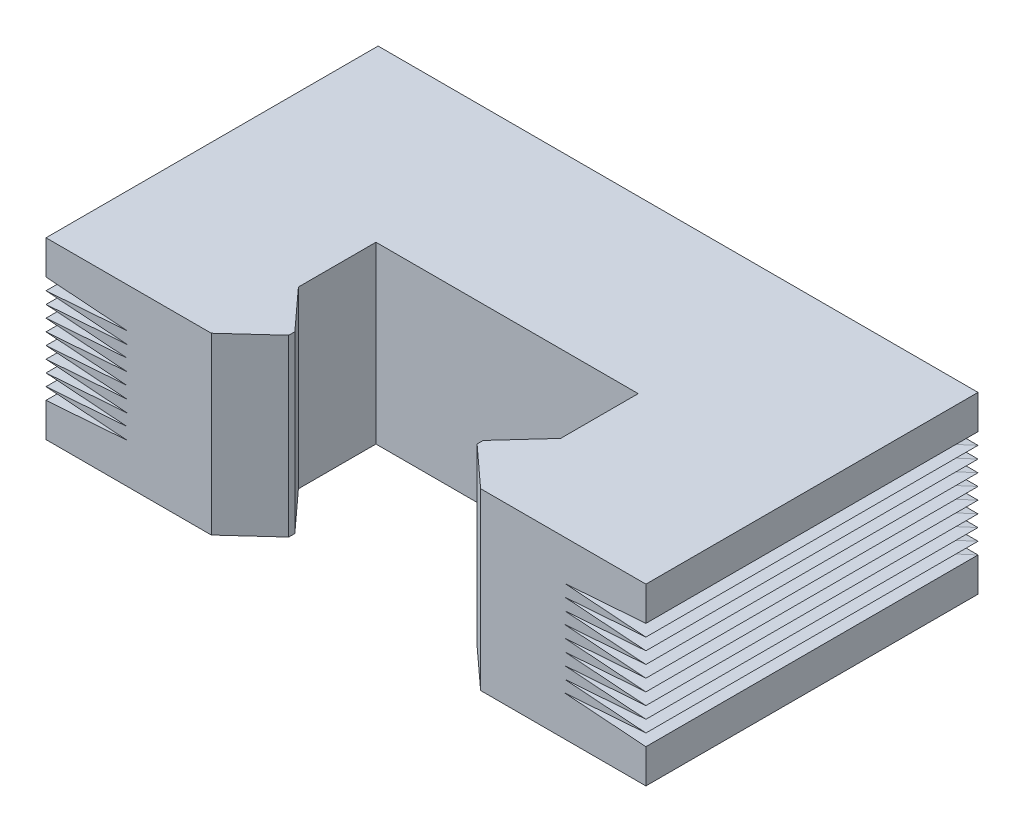
SolidWorks part; units mm, degrees
ref_plane "Front Plane" through (0, 0, 0) normal (0, 0, 1) x (1, 0, 0)
ref_plane "Top Plane" through (0, 0, 0) normal (0, 1, 0) x (1, 0, 0)
ref_plane "Right Plane" through (0, 0, 0) normal (1, 0, 0) x (0, 0, -1)
sketch "Sketch3" plane through (0, 0, 0) normal (0, 1, 0) x (1, 0, 0)
  line L0 (0, 0) -> (0, 15.96) construction
  line L1 (-28, 15.96) -> (28, 15.96)
  line L2 (28, 15.96) -> (28, -15.04)
  line L3 (28, -15.04) -> (12.57, -15.04)
  line L4 (12.57, -15.04) -> (8.79, -11.59)
  line L5 (8.79, -11.59) -> (8.79, -11.02)
  line L6 (8.79, -11.02) -> (12.24, -7.24)
  line L7 (12.24, -7.24) -> (12.24, 0)
  line L8 (12.24, 0) -> (-12.24, 0)
  line L9 (-12.24, -7.24) -> (-12.24, 0)
  line L10 (-8.79, -11.02) -> (-12.24, -7.24)
  line L11 (-8.79, -11.59) -> (-8.79, -11.02)
  line L12 (-12.57, -15.04) -> (-8.79, -11.59)
  line L13 (-28, -15.04) -> (-12.57, -15.04)
  line L14 (-28, 15.96) -> (-28, -15.04)
  point P12 (0, 0)
  point P18 (12.24, 7.1402)
  point P19 (0, 0)
  dimension "D1" = 56
  dimension "D2" = 31
  dimension "D3" = 24.48
  dimension "D4" = 15.04
  dimension "D5" = 0.57
  dimension "D6" = 15.43
  dimension "D7" = 7.8
  dimension "D8" = 15.76
  dimension "D9" = 3.78
sketch "Sketch4" plane through (0, 0, 0) normal (0, 0, 1) x (1, 0, 0)
  line L0 (28, 0) -> (28, -3.175)
  line L1 (28, 0) -> (12.57, 0) construction
  line L2 (28, -3.175) -> (20.4001, -3.7287)
  line L3 (20.4001, -3.7287) -> (28, -4.2824)
  line L4 (28, -4.2824) -> (20.4001, -4.8361)
  line L5 (20.4001, -4.8361) -> (28, -5.3898)
  line L6 (28, -5.3898) -> (20.4001, -5.9435)
  line L7 (20.4001, -5.9435) -> (28, -6.4972)
  line L8 (28, -6.4972) -> (20.4001, -7.051)
  line L9 (20.4001, -7.051) -> (28, -7.6047)
  line L10 (28, -7.6047) -> (20.4001, -8.1584)
  line L11 (20.4001, -8.1584) -> (28, -8.7121)
  line L12 (28, -8.7121) -> (20.4001, -9.2658)
  line L13 (20.4001, -9.2658) -> (28, -9.8195)
  line L14 (28, -9.8195) -> (20.4001, -10.3732)
  line L15 (20.4001, -10.3732) -> (28, -10.9269)
  line L16 (28, -10.9269) -> (20.4001, -11.4806)
  line L17 (20.4001, -11.4806) -> (28, -12.0343)
  line L18 (28, -12.0343) -> (20.4001, -12.588)
  line L19 (20.4001, -12.588) -> (28, -13.1417)
  line L20 (28, -13.1417) -> (28, -16.3167)
  line L21 (0, 0) -> (0, -16.3167) construction
  line L22 (-28, -13.1417) -> (-28, -16.3167)
  line L23 (-20.4001, -12.588) -> (-28, -13.1417)
  line L24 (-28, -12.0343) -> (-20.4001, -12.588)
  line L25 (-20.4001, -11.4806) -> (-28, -12.0343)
  line L26 (-28, -10.9269) -> (-20.4001, -11.4806)
  line L27 (-20.4001, -10.3732) -> (-28, -10.9269)
  line L28 (-28, -9.8195) -> (-20.4001, -10.3732)
  line L29 (-20.4001, -9.2658) -> (-28, -9.8195)
  line L30 (-28, -8.7121) -> (-20.4001, -9.2658)
  line L31 (-20.4001, -8.1584) -> (-28, -8.7121)
  line L32 (-28, -7.6047) -> (-20.4001, -8.1584)
  line L33 (-20.4001, -7.051) -> (-28, -7.6047)
  line L34 (-28, -6.4972) -> (-20.4001, -7.051)
  line L35 (-20.4001, -5.9435) -> (-28, -6.4972)
  line L36 (-28, -5.3898) -> (-20.4001, -5.9435)
  line L37 (-20.4001, -4.8361) -> (-28, -5.3898)
  line L38 (-28, -4.2824) -> (-20.4001, -4.8361)
  line L39 (-20.4001, -3.7287) -> (-28, -4.2824)
  line L40 (-28, -3.175) -> (-20.4001, -3.7287)
  line L41 (-28, 0) -> (-28, -3.175)
  line L42 (28, -3.175) -> (28, -4.2824)
  line L43 (28, -5.3898) -> (28, -6.4972)
  line L44 (28, -7.6047) -> (28, -8.7121)
  line L45 (28, -4.2824) -> (28, -5.3898)
  line L46 (28, -6.4972) -> (28, -7.6047)
  line L47 (28, -8.7121) -> (28, -9.8195)
  line L48 (28, -10.9269) -> (28, -9.8195)
  line L49 (28, -10.9269) -> (28, -12.0343)
  line L50 (28, -12.0343) -> (28, -13.1417)
  line L51 (-28, -13.1417) -> (-28, -12.0343)
  line L52 (-28, -10.9269) -> (-28, -12.0343)
  line L53 (-28, -10.9269) -> (-28, -9.8195)
  line L54 (-28, -8.7121) -> (-28, -9.8195)
  line L55 (-28, -7.6047) -> (-28, -8.7121)
  line L56 (-28, -6.4972) -> (-28, -7.6047)
  line L57 (-28, -5.3898) -> (-28, -6.4972)
  line L58 (-28, -4.2824) -> (-28, -5.3898)
  line L59 (-28, -3.175) -> (-28, -4.2824)
  dimension "D1" = 3.175
  dimension "D2" = 7.62
sketch "Sketch5" plane through (0, 0, 0) normal (1, 0, 0) x (0, 0, -1)
  line L0 (15.96, 0) -> (15.96, -3.175)
  line L1 (0, 0) -> (15.96, 0) construction
  line L2 (15.96, -3.175) -> (8.3601, -3.7287)
  line L3 (8.3601, -3.7287) -> (15.96, -4.2824)
  line L4 (15.96, -4.2824) -> (8.3601, -4.8361)
  line L5 (8.3601, -4.8361) -> (15.96, -5.3898)
  line L6 (15.96, -5.3898) -> (8.3601, -5.9435)
  line L7 (8.3601, -5.9435) -> (15.96, -6.4972)
  line L8 (15.96, -6.4972) -> (8.3601, -7.051)
  line L9 (8.3601, -7.051) -> (15.96, -7.6047)
  line L10 (15.96, -7.6047) -> (8.3601, -8.1584)
  line L11 (8.3601, -8.1584) -> (15.96, -8.7121)
  line L12 (15.96, -8.7121) -> (8.3601, -9.2658)
  line L13 (8.3601, -9.2658) -> (15.96, -9.8195)
  line L14 (15.96, -9.8195) -> (8.3601, -10.3732)
  line L15 (8.3601, -10.3732) -> (15.96, -10.9269)
  line L16 (15.96, -10.9269) -> (8.3601, -11.4806)
  line L17 (8.3601, -11.4806) -> (15.96, -12.0343)
  line L18 (15.96, -12.0343) -> (8.3601, -12.588)
  line L19 (8.3601, -12.588) -> (15.96, -12.0343)
  line L20 (15.96, -3.175) -> (15.96, -4.2824)
  line L21 (15.96, -5.3898) -> (15.96, -6.4972)
  line L22 (8.3601, -12.588) -> (15.96, -13.1417)
  line L23 (15.96, -13.1417) -> (15.96, -16.3167)
  line L24 (15.96, -7.6047) -> (15.96, -8.7121)
  line L25 (15.96, -9.8195) -> (15.96, -10.9269)
  line L26 (15.96, -12.0343) -> (15.96, -13.1417)
  line L27 (15.96, -12.0343) -> (15.96, -10.9269)
  line L28 (15.96, -9.8195) -> (15.96, -8.7121)
  line L29 (15.96, -7.6047) -> (15.96, -6.4972)
  line L30 (15.96, -5.3898) -> (15.96, -4.2824)
  dimension "D1" = 3.175
  dimension "D2" = 7.62
extrude "Boss-Extrude1" add sketch "Sketch3" against normal up to vertex (16.3167 mm away) up to point (28, -16.3167, 0)
extrude "Cut-Extrude1" cut sketch "Sketch4" against normal through all both and the other way through all contours L42 L2 L3 | L45 L4 L5 | L43 L6 L7 | L46 L8 L9 | L44 L10 L11 | L47 L12 L13 | L15 L48 L14 | L49 L16 L17 | L50 L18 L19 | L51 L23 L24 | L26 L52 L25 | L53 L27 L28 | L30 L54 L29 | L32 L55 L31 | L34 L56 L33 | L36 L57 L35 | L38 L58 L37 | L40 L59 L39
extrude "Cut-Extrude2" cut sketch "Sketch5" against normal through all both and the other way through all contours L20 L2 L3 | L5 L30 L4 | L21 L6 L7 | L9 L29 L8 | L24 L10 L11 | L13 L28 L12 | L25 L14 L15 | L17 L27 L16 | L26 L18 L22
